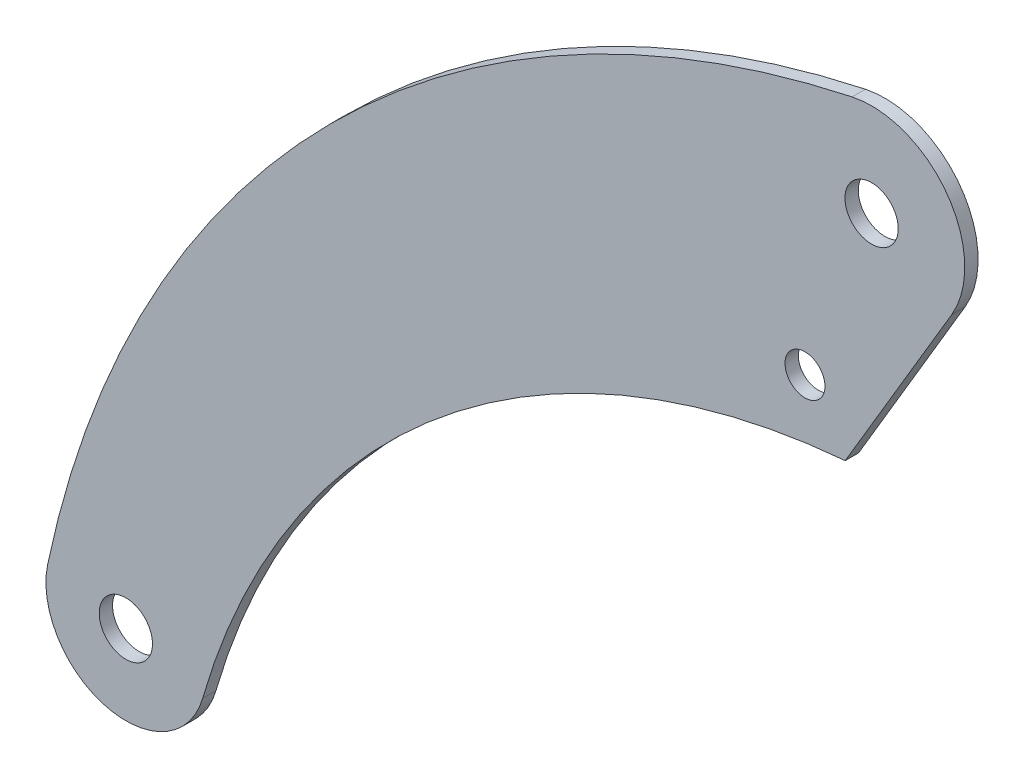
SolidWorks part; units mm, degrees
ref_plane "Front Plane" through (0, 0, 0) normal (0, 0, 1) x (1, 0, 0)
ref_plane "Top Plane" through (0, 0, 0) normal (0, 1, 0) x (1, 0, 0)
ref_plane "Right Plane" through (0, 0, 0) normal (1, 0, 0) x (0, 0, -1)
sketch "Sketch1" plane through (0, 0, 0) normal (0, 0, 1) x (1, 0, 0)
  line L0 (60.2204, -35.6862) -> (-19.7796, -170.6862)
  circle A0 centre (0, 0) radius 20
  circle A1 centre (-50, -130) radius 15
  circle A2 centre (-560, -550) radius 20
  arc A3 (60.2204, -35.6862) -> (-14.6346, 68.4531) centre (0, 0) ccw
  arc A4 (-502.3419, -566.5995) -> (-618.7157, -537.6524) centre (-560, -550) cw
  arc A5 (-19.7796, -170.6862) -> (-502.3419, -566.5995) centre (26.1907, -718.7616) ccw
  arc A6 (-14.6346, 68.4531) -> (-618.7157, -537.6524) centre (149.4818, -699.1997) ccw
  dimension "D1" = 40
  dimension "D2" = 30
  dimension "D3" = 40
  dimension "D4" = 130
  dimension "D5" = 50
  dimension "D6" = 550
  dimension "D7" = 560
  dimension "D8" = 60
  dimension "D9" = 70
  dimension "D10" = 135
  dimension "D12" = 550
  dimension "D13" = 785
  dimension "D11" = 80
extrude "Boss-Extrude1" add sketch "Sketch1" along normal mid plane 10
